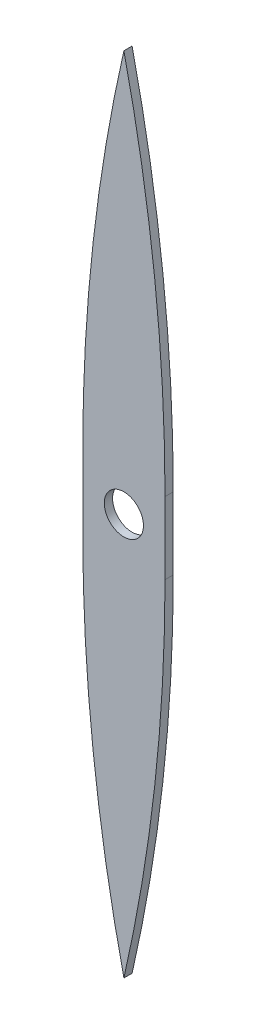
SolidWorks part; units mm, degrees
ref_plane "Front Plane" through (0, 0, 0) normal (0, 0, 1) x (1, 0, 0)
ref_plane "Top Plane" through (0, 0, 0) normal (0, 1, 0) x (1, 0, 0)
ref_plane "Right Plane" through (0, 0, 0) normal (1, 0, 0) x (0, 0, -1)
sketch "Sketch2" plane through (0, 0, 0) normal (0, 0, 1) x (1, 0, 0)
  line L2 (-10, -3.6796) -> (-10, 13.8204)
  line L4 (10, -3.6796) -> (10, 13.8204)
  line L5 (-0.0013, -92.5559) -> (0.0013, -92.5559)
  arc A0 (-10, 13.8204) -> (0, 102.7023) centre (390, 13.8204) cw
  arc A2 (10, 13.8204) -> (0, 102.7023) centre (-390, 13.8204) ccw
  arc A3 (10, -3.6796) -> (0.0013, -92.5559) centre (-390, -3.6796) cw
  arc A4 (-10, -3.6796) -> (-0.0013, -92.5559) centre (390, -3.6796) ccw
  point P0 (0, 2.7023)
  point P11 (0, 0)
  point P16 (0, 0)
extrude "Boss-Extrude1" add sketch "Sketch2" along normal blind 2
sketch "Sketch9" plane through (0, 0, 0) normal (0, 0, -1) x (-1, 0, 0)
  circle A0 centre (-0.0007, 5.0732) radius 4.76
  point P12 (0, 0)
  point P13 (0, -92.5559)
  point P14 (0, -92.5559)
extrude "Cut-Extrude1" cut sketch "Sketch9" against normal blind 16 and the other way blind 15
